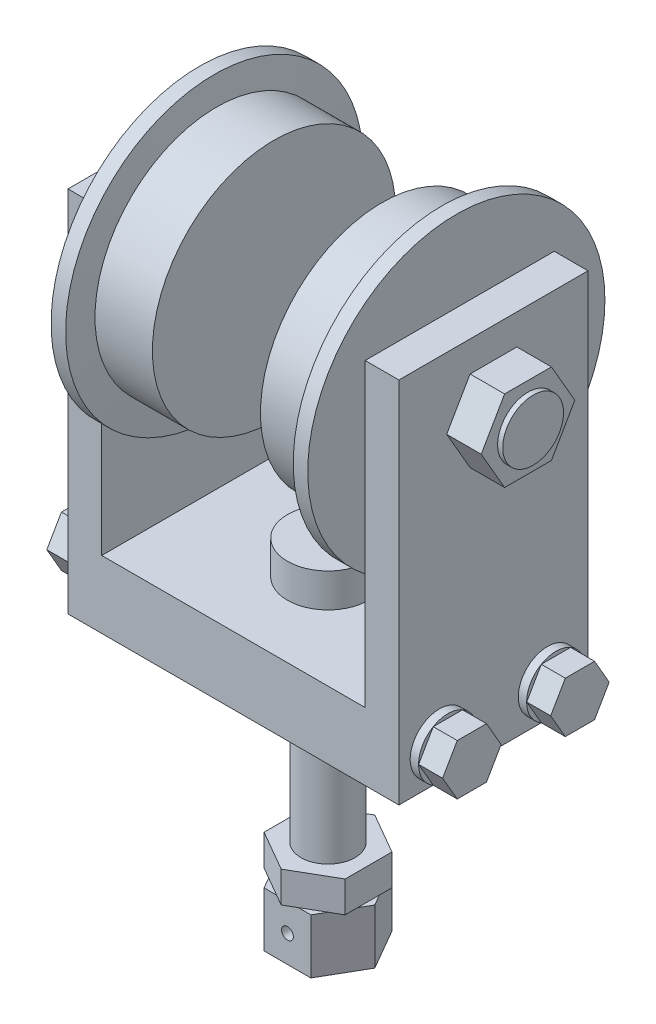
SolidWorks part; units mm, degrees
ref_plane "Front" through (0, 0, 0) normal (0, 0, 1) x (1, 0, 0)
ref_plane "Top" through (0, 0, 0) normal (0, 1, 0) x (1, 0, 0)
ref_plane "Right" through (0, 0, 0) normal (1, 0, 0) x (0, 0, -1)
ref_plane "Z PLANE" through (0, 0, 0) normal (0, 0, 1) x (1, 0, 0)
ref_plane "YOKE BOTTOM" through (0, 0, 0) normal (0, 1, 0) x (-1, 0, 0)
ref_plane "X PLANE" through (0, 0, 0) normal (1, 0, 0) x (0, 0, -1)
sketch "YOKE CROSS SECTION" plane through (0, 0, 0) normal (1, 0, 0) x (0, 0, -1)
  line L0 (0, 0) -> (0, 57.0916) construction
  line L1 (0, 84.8167) -> (0, -84.8167) construction
  line L2 (-44.45, 0) -> (44.45, 0)
  line L3 (69.1602, 0) -> (-69.1602, 0) construction
  line L4 (44.45, 0) -> (44.45, 31.75)
  line L5 (-44.45, 0) -> (-44.45, 31.75)
  line L6 (44.45, 31.75) -> (-44.45, 31.75)
  point P12 (0, 31.75)
  dimension "D1" = 31.75
  dimension "D2" = 88.9
ref_plane "1/2 YOKE LENGTH (A)" through (61.9125, 0, 0) normal (1, 0, 0) x (0, 0, -1)
extrude "YOKE" add sketch "YOKE CROSS SECTION" along normal up to surface (61.9125 mm away) up to plane "1/2 YOKE LENGTH (A)"
sketch "SIDEPLATE PROFILE" plane through (61.9125, 0, 0) normal (1, 0, 0) x (0, 0, -1)
  line L0 (0, 0) -> (0, 74.7424) construction
  line L1 (0, 84.8167) -> (0, -84.8167) construction
  line L2 (-44.45, 0) -> (44.45, 0)
  line L3 (44.45, 0) -> (44.45, 173.0375)
  line L4 (-44.45, 0) -> (-44.45, 173.0375)
  line L5 (44.45, 173.0375) -> (-44.45, 173.0375)
  point P11 (0, 173.0375)
  dimension "D1" = 173.0375
ref_plane "WHEEL HEIGHT" through (0, 139.7, 0) normal (0, 1, 0) x (-1, 0, 0)
ref_plane "SCREW LOCATION X" through (0, 0, 25.4) normal (0, 0, 1) x (1, 0, 0)
ref_plane "SCREW LOCATION Y" through (0, 15.875, 0) normal (0, 1, 0) x (-1, 0, 0)
extrude "SIDEPLATE" add sketch "SIDEPLATE PROFILE" along normal blind 15.875
sketch "WHEEL PIN NUT PROFILE" plane through (77.7875, 0, 0) normal (1, 0, 0) x (0, 0, -1)
  line L0 (0, 84.8167) -> (0, -84.8167) construction
  line L1 (21.997, 139.7) -> (10.9985, 158.75)
  line L2 (10.9985, 158.75) -> (-10.9985, 158.75)
  line L3 (-10.9985, 158.75) -> (-21.997, 139.7)
  line L4 (-21.997, 139.7) -> (-10.9985, 120.65)
  line L5 (-10.9985, 120.65) -> (10.9985, 120.65)
  line L6 (10.9985, 120.65) -> (21.997, 139.7)
  line L7 (69.1602, 139.7) -> (-69.1602, 139.7) construction
  circle A0 centre (0, 139.7) radius 19.05 construction
  dimension "D1" = 38.1
extrude "WHEEL PIN NUT" add sketch "WHEEL PIN NUT PROFILE" along normal blind 16.2306
sketch "WHEEL PIN PROJECTION PROFILE" plane through (94.0181, 0, 0) normal (1, 0, 0) x (0, 0, -1)
  line L0 (0, 84.8167) -> (0, -84.8167) construction
  line L1 (69.1602, 139.7) -> (-69.1602, 139.7) construction
  circle A0 centre (0, 139.7) radius 14.2875
  dimension "D1" = 28.575
extrude "WHEEL PIN PROJECTION" add sketch "WHEEL PIN PROJECTION PROFILE" along normal blind 2.413
sketch "LOCKNUTS PROFILE" plane through (77.7875, 0, 0) normal (1, 0, 0) x (0, 0, -1)
  line L0 (-25.4, 84.8167) -> (-25.4, -84.8167) construction
  line L1 (50, 15.875) -> (-50, 15.875) construction
  circle A0 centre (-25.4, 15.875) radius 13.7541
  dimension "D1" = 27.5082
extrude "LOCKNUTS" add sketch "LOCKNUTS PROFILE" along normal blind 3.9624
sketch "SCREWS PROFILE" plane through (81.7499, 0, 0) normal (1, 0, 0) x (0, 0, -1)
  line L0 (50, 15.875) -> (-50, 15.875) construction
  line L1 (-11.6518, 15.875) -> (-18.5259, 27.7812)
  line L2 (-18.5259, 27.7812) -> (-32.2741, 27.7812)
  line L3 (-32.2741, 27.7812) -> (-39.1482, 15.875)
  line L4 (-39.1482, 15.875) -> (-32.2741, 3.9688)
  line L5 (-32.2741, 3.9688) -> (-18.5259, 3.9688)
  line L6 (-18.5259, 3.9688) -> (-11.6518, 15.875)
  line L7 (-25.4, 84.8167) -> (-25.4, -84.8167) construction
  circle A0 centre (-25.4, 15.875) radius 11.9062 construction
  dimension "D1" = 23.8125
extrude "SCREWS" add sketch "SCREWS PROFILE" along normal blind 11.2776
sketch "PROFILE" plane through (0, 31.75, 0) normal (0, 1, 0) x (-1, 0, 0)
  line L0 (84.8167, 0) -> (-84.8167, 0) construction
  line L1 (0, 83.2389) -> (0, -83.2389) construction
  circle A0 centre (0, 0) radius 19.05
  dimension "D1" = 38.1
extrude "KING BOLT HEAD" add sketch "PROFILE" along normal blind 15.875
mirror "Mirror1" about plane through (0, 0, 0) normal (0, 0, 1) of "SCREWS", "LOCKNUTS"
mirror "Mirror5" about plane through (0, 0, 0) normal (1, 0, 0) of bodies 112
ref_plane "TOP OF NUT" through (0, -76.2, 0) normal (0, 1, 0) x (-1, 0, 0)
sketch "DIA." plane through (0, 0, 0) normal (0, -1, 0) x (1, 0, 0)
  line L0 (84.8167, 0) -> (-84.8167, 0) construction
  line L1 (0, -83.2389) -> (0, 83.2389) construction
  circle A0 centre (0, 0) radius 12.7
  dimension "D1" = 25.4
extrude "KING BOLT" add sketch "DIA." along normal up to surface (76.2 mm away) up to plane "TOP OF NUT"
sketch "KING BOLT JAN NUT PROFILE" plane through (0, -76.2, 0) normal (0, -1, 0) x (1, 0, 0)
  line L0 (84.8167, 0) -> (-84.8167, 0) construction
  line L1 (0, -21.997) -> (19.05, -10.9985)
  line L2 (19.05, -10.9985) -> (19.05, 10.9985)
  line L3 (19.05, 10.9985) -> (0, 21.997)
  line L4 (0, 21.997) -> (-19.05, 10.9985)
  line L5 (-19.05, 10.9985) -> (-19.05, -10.9985)
  line L6 (-19.05, -10.9985) -> (0, -21.997)
  line L7 (0, -83.2389) -> (0, 83.2389) construction
  circle A0 centre (0, 0) radius 19.05 construction
  dimension "D1" = 38.1
extrude "KING BOLT JAM NUT" add sketch "KING BOLT JAN NUT PROFILE" along normal blind 14.605
sketch "KING BOLT NUT PROFILE" plane through (0, -90.805, 0) normal (0, -1, 0) x (1, 0, 0)
  line L1 (21.997, 0) -> (10.9985, 19.05)
  line L2 (10.9985, 19.05) -> (-10.9985, 19.05)
  line L3 (-10.9985, 19.05) -> (-21.997, 0)
  line L4 (-21.997, 0) -> (-10.9985, -19.05)
  line L5 (-10.9985, -19.05) -> (10.9985, -19.05)
  line L6 (10.9985, -19.05) -> (21.997, 0)
  line L10 (0, -83.2389) -> (0, 83.2389) construction
  line L11 (84.8167, 0) -> (-84.8167, 0) construction
  circle A0 centre (0, 0) radius 19.05 construction
  dimension "D1" = 38.1
extrude "KING BOLT NUT" add sketch "KING BOLT NUT PROFILE" along normal blind 25.7048
sketch "Sketch5" plane through (0, -116.5098, 0) normal (0, -1, 0) x (1, 0, 0)
  circle A0 centre (0, 0) radius 12.7 construction
  circle A1 centre (0, 0) radius 12.7
extrude "EXTENDED KING BOLT" add sketch "Sketch5" along normal blind 6.35
chamfer "Chamfer1" distance 2.3812 angle 45 1 edges at (0, -122.8598, -12.7)
ref_plane "MOUNTING REF PLANE" through (0, -34.925, 0) normal (0, 1, 0) x (-1, 0, 0)
sketch "Sketch7" plane through (0, 0, 0) normal (0, 0, 1) x (1, 0, 0)
  line L0 (60.325, 155.575) -> (60.325, 209.55)
  line L1 (52.3875, 196.85) -> (53.4986, 209.55)
  line L2 (25.4, 139.7) -> (25.4, 196.85)
  line L3 (61.9125, 139.7) -> (25.4, 139.7)
  line L4 (61.9125, 155.575) -> (61.9125, 139.7)
  line L5 (61.9125, 155.575) -> (60.325, 155.575)
  line L6 (60.325, 209.55) -> (53.4986, 209.55)
  line L7 (52.3875, 196.85) -> (25.4, 196.85)
  dimension "D1" = 34.925
  dimension "D2" = 12.7485
  dimension "D4" = 15.875
  dimension "D5" = 1.5875
  dimension "D6" = 6.8264
  dimension "D7" = 69.85
  dimension "D8" = 12.7
revolve "WHEEL" add sketch "Sketch7" angle 360 about L3
mirror "Mirror6" about plane through (0, 0, 0) normal (1, 0, 0) of "WHEEL"
sketch "Sketch8" plane through (0, 0, 19.05) normal (0, 0, 1) x (1, 0, 0)
  line L0 (0, -82.9507) -> (0, 82.9507) construction
  line L1 (-10.9985, -116.5098) -> (-21.997, -116.5098) construction
  circle A0 centre (0, -103.8098) radius 2.7686
  dimension "D2" = 5.5372
  dimension "D1" = 12.7
extrude "COTTER PIN HOLE" cut sketch "Sketch8" against normal up to next
sketch "Sketch9" plane through (0, 0, 0) normal (0, -1, 0) x (1, 0, 0)
  circle A0 centre (0, 0) radius 25.4
  circle A1 centre (0, 0) radius 30.1625
  dimension "D1" = 50.8
  dimension "D2" = 60.325
extrude "SPACER" [suppressed] add sketch "Sketch9" along normal blind 12.7
ref_plane "TREAD OF TRACK" through (0, 82.55, 0) normal (0, 1, 0) x (-1, 0, 0)
